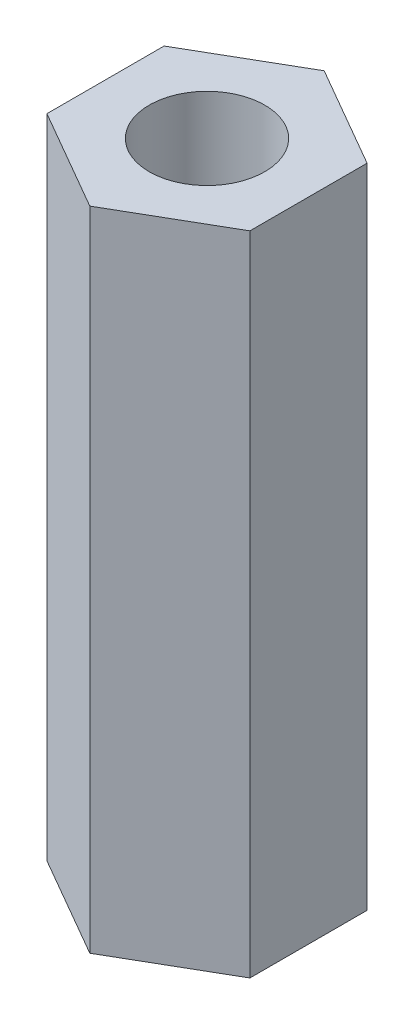
SolidWorks part; units mm, degrees
ref_plane "Спереди" through (0, 0, 0) normal (0, 0, 1) x (1, 0, 0)
ref_plane "Сверху" through (0, 0, 0) normal (0, 1, 0) x (1, 0, 0)
ref_plane "Справа" through (0, 0, 0) normal (1, 0, 0) x (0, 0, -1)
sketch "Эскиз1" plane through (0, 0, 0) normal (0, 1, 0) x (1, 0, 0)
  line L1 (0, 3.0426) -> (-2.635, 1.5213)
  line L2 (-2.635, 1.5213) -> (-2.635, -1.5213)
  line L3 (-2.635, -1.5213) -> (0, -3.0426)
  line L4 (0, -3.0426) -> (2.635, -1.5213)
  line L5 (2.635, -1.5213) -> (2.635, 1.5213)
  line L6 (2.635, 1.5213) -> (0, 3.0426)
  circle A0 centre (0, 0) radius 2.635 construction
  circle A1 centre (0, 0) radius 1.5
  dimension "D1" = 3
  dimension "D2" = 5.27
extrude "Бобышка-Вытянуть1" add sketch "Эскиз1" along normal blind 16.8
